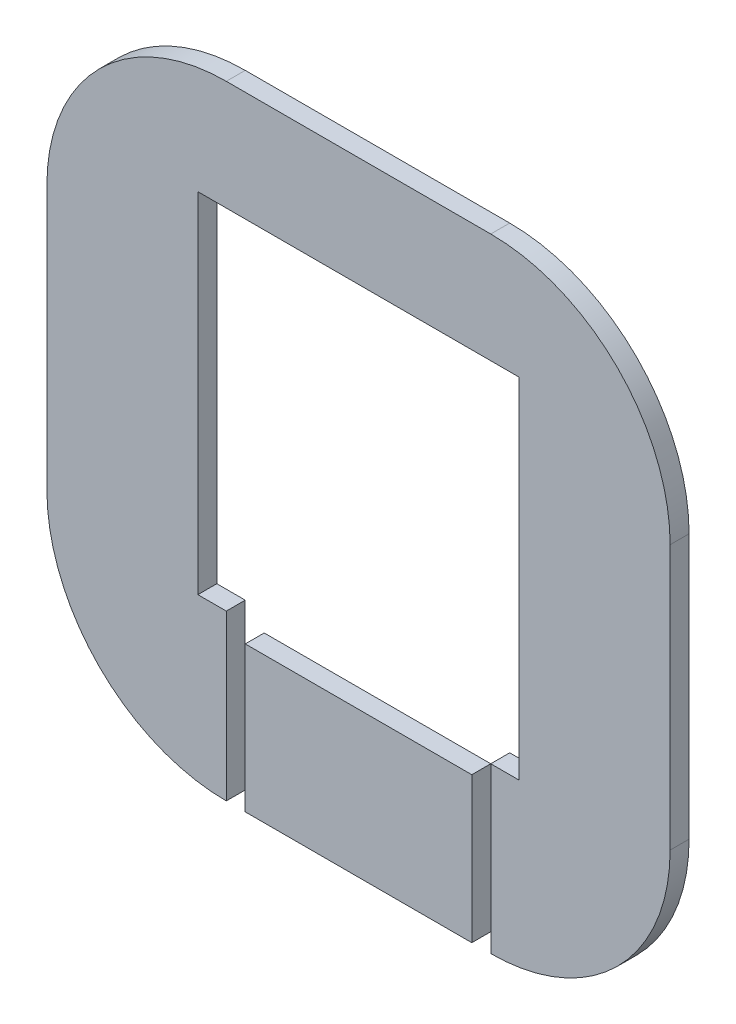
SolidWorks part; units mm, degrees
ref_plane "Front Plane" through (0, 0, 0) normal (0, 0, 1) x (1, 0, 0)
ref_plane "Top Plane" through (0, 0, 0) normal (0, 1, 0) x (1, 0, 0)
ref_plane "Right Plane" through (0, 0, 0) normal (1, 0, 0) x (0, 0, -1)
sketch "Sketch1" plane through (0, 0, 0) normal (0, 0, 1) x (1, 0, 0)
  line L0 (0, 53.5) -> (0, -96.5) construction
  line L1 (-75, 53.5) -> (75, 53.5) construction
  line L2 (-75, 53.5) -> (-75, -96.5) construction
  line L3 (-75, -96.5) -> (75, -96.5) construction
  line L4 (75, 53.5) -> (75, -96.5) construction
  line L5 (-30, 53.5) -> (30, 53.5) construction
  line L6 (-30, -96.5) -> (30, -96.5) construction
  line L7 (-75, 8.5) -> (75, 8.5) construction
  line L8 (-75, 8.5) -> (-75, -51.5) construction
  line L9 (-75, -51.5) -> (75, -51.5) construction
  line L10 (75, 8.5) -> (75, -51.5) construction
  line L11 (-30, -96.5) -> (-0.5, -96.5) construction
  line L12 (0.5, -96.5) -> (30, -96.5) construction
  line L13 (-0.5, -96.5) -> (0.5, -96.5) construction
  line L14 (-0.5, -92.2) -> (0.5, -92.2)
  line L15 (0.5, -92.2) -> (30, -92.2)
  line L16 (70.7, 8.5) -> (70.7, -51.5)
  line L17 (-30, 49.2) -> (30, 49.2)
  line L18 (-70.7, 8.5) -> (-70.7, -51.5)
  line L19 (-30, -92.2) -> (-0.5, -92.2)
  arc A0 (-75, 8.5) -> (-30, 53.5) centre (-30, 8.5) cw construction
  arc A1 (30, 53.5) -> (75, 8.5) centre (30, 8.5) cw construction
  arc A2 (-75, -51.5) -> (-30, -96.5) centre (-30, -51.5) ccw construction
  arc A3 (30, -96.5) -> (75, -51.5) centre (30, -51.5) ccw construction
  arc A4 (30, -92.2) -> (70.7, -51.5) centre (30, -51.5) ccw
  arc A5 (30, 49.2) -> (70.7, 8.5) centre (30, 8.5) cw
  arc A6 (-70.7, 8.5) -> (-30, 49.2) centre (-30, 8.5) cw
  arc A7 (-70.7, -51.5) -> (-30, -92.2) centre (-30, -51.5) ccw
  point P10 (0, 53.5)
  point P19 (0, -96.5)
  dimension "D3" = 45
  dimension "D4" = 45
  dimension "D1" = 150
  dimension "D2" = 150
  dimension "D5" = 8.5
  dimension "D6" = 4.3
extrude "Boss-Extrude1" add sketch "Sketch1" along normal blind 4.3
sketch "Sketch2" plane through (0, 0, 4.3) normal (0, 0, 1) x (1, 0, 0)
  line L0 (-30, -92.2) -> (30, -92.2) construction
  line L1 (-30, -92.2) -> (-25.7, -92.2)
  line L2 (-30, -92.2) -> (-30, -59.19)
  line L3 (-30, -59.19) -> (-25.7, -59.19)
  line L4 (-25.7, -92.2) -> (-25.7, -59.19)
  line L6 (-30, -59.19) -> (30, -59.19)
  line L7 (-30, -59.19) -> (-30, -54.89)
  line L8 (-30, -54.89) -> (30, -54.89)
  line L9 (30, -59.19) -> (30, -54.89)
  line L10 (30, -59.19) -> (25.7, -59.19)
  line L11 (30, -59.19) -> (30, -92.2)
  line L12 (30, -92.2) -> (25.7, -92.2)
  line L13 (25.7, -59.19) -> (25.7, -92.2)
  line L14 (-36.45, 24.29) -> (36.45, 24.29)
  line L15 (-36.45, 24.29) -> (-36.45, -54.89)
  line L16 (-36.45, -54.89) -> (36.45, -54.89)
  line L17 (36.45, 24.29) -> (36.45, -54.89)
  point P12 (0, -54.89)
  point P18 (0, 24.29)
  line M15 (-30, -92.2) -> (30, -92.2)
  dimension "D1" = 4.3
  dimension "D2" = 4.3
  dimension "D3" = 4.3
  dimension "D4" = 60
  dimension "D5" = 33.01
  dimension "D6" = 79.18
  dimension "D7" = 72.9
extrude "Cut-Extrude1" cut sketch "Sketch2" against normal up to vertex (4.3 mm away) contours L17 L14 L15 L16 L8 | L6 L9 L8 L7 L3 | L4 L3 L2 M15 | L11 L12 L13 L10 up to point (0, 0, 0)
